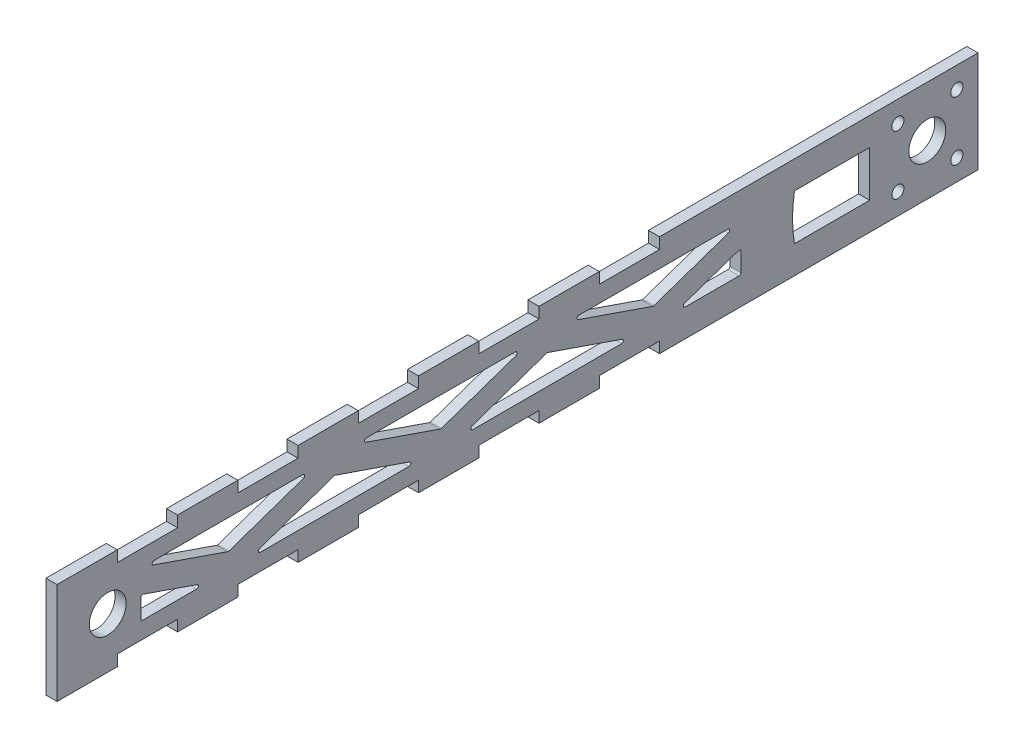
SolidWorks part; units mm, degrees
other "Markup1"
sketch "Sketch2" plane through (3, 13.75, 150) normal (0.7954, 0.3724, 0.4781) x (0.4726, 0.1125, -0.874)
ref_plane "Front Plane" through (0, 0, 0) normal (0, 0, 1) x (1, 0, 0)
ref_plane "Top Plane" through (0, 0, 0) normal (0, 1, 0) x (1, 0, 0)
ref_plane "Right Plane" through (0, 0, 0) normal (1, 0, 0) x (0, 0, -1)
sketch "Sketch1" plane through (0, 0, 0) normal (1, 0, 0) x (0, 0, -1)
  line L0 (71.25, -13.75) -> (71.25, 13.75) construction
  line L1 (-125, -13.75) -> (125, -13.75)
  line L2 (-125, -13.75) -> (-125, 13.75)
  line L3 (-125, 13.75) -> (125, 13.75)
  line L4 (125, -13.75) -> (125, 13.75)
  line L5 (-125, -13.75) -> (125, 13.75) construction
  line L6 (-125, 13.75) -> (125, -13.75) construction
  line L7 (103.25, -8) -> (119.25, -8) construction
  line L8 (103.25, -8) -> (103.25, 8) construction
  line L9 (103.25, 8) -> (119.25, 8) construction
  line L10 (119.25, -8) -> (119.25, 8) construction
  line L11 (103.25, -8) -> (119.25, 8) construction
  line L12 (103.25, 8) -> (119.25, -8) construction
  line L13 (-125, 10.75) -> (-108.6458, 10.75) construction
  line L14 (-108.6458, 10.75) -> (-92.2917, 10.75)
  line L15 (-108.6458, 10.75) -> (-108.6458, 13.75)
  line L16 (-108.6458, 13.75) -> (-92.2917, 13.75)
  line L17 (-92.2917, 10.75) -> (-92.2917, 13.75)
  line L18 (-108.6458, 10.75) -> (-92.2917, 13.75) construction
  line L19 (-108.6458, 13.75) -> (-92.2917, 10.75) construction
  line L20 (-75.9375, 10.75) -> (-59.5833, 10.75)
  line L21 (-75.9375, 10.75) -> (-75.9375, 13.75)
  line L22 (-75.9375, 13.75) -> (-59.5833, 13.75)
  line L23 (-59.5833, 10.75) -> (-59.5833, 13.75)
  line L24 (-75.9375, 10.75) -> (-59.5833, 13.75) construction
  line L25 (-75.9375, 13.75) -> (-59.5833, 10.75) construction
  line L26 (-43.2292, 10.75) -> (-26.875, 10.75)
  line L27 (-43.2292, 10.75) -> (-43.2292, 13.75)
  line L28 (-43.2292, 13.75) -> (-26.875, 13.75)
  line L29 (-26.875, 10.75) -> (-26.875, 13.75)
  line L30 (-43.2292, 10.75) -> (-26.875, 13.75) construction
  line L31 (-43.2292, 13.75) -> (-26.875, 10.75) construction
  line L32 (-10.5208, 10.75) -> (5.8333, 10.75)
  line L33 (-10.5208, 10.75) -> (-10.5208, 13.75)
  line L34 (-10.5208, 13.75) -> (5.8333, 13.75)
  line L35 (5.8333, 10.75) -> (5.8333, 13.75)
  line L36 (-10.5208, 10.75) -> (5.8333, 13.75) construction
  line L37 (-10.5208, 13.75) -> (5.8333, 10.75) construction
  line L38 (22.1875, 10.75) -> (38.5417, 10.75)
  line L39 (22.1875, 10.75) -> (22.1875, 13.75)
  line L40 (22.1875, 13.75) -> (38.5417, 13.75)
  line L41 (38.5417, 10.75) -> (38.5417, 13.75)
  line L42 (22.1875, 10.75) -> (38.5417, 13.75) construction
  line L43 (22.1875, 13.75) -> (38.5417, 10.75) construction
  line L44 (54.8958, 10.75) -> (71.25, 10.75)
  line L45 (54.8958, 10.75) -> (54.8958, 13.75)
  line L46 (54.8958, 13.75) -> (71.25, 13.75)
  line L47 (71.25, 10.75) -> (71.25, 13.75)
  line L48 (54.8958, 10.75) -> (71.25, 13.75) construction
  line L49 (54.8958, 13.75) -> (71.25, 10.75) construction
  line L50 (-92.2917, 10.75) -> (-75.9375, 10.75) construction
  line L51 (-59.5833, 10.75) -> (-43.2292, 10.75) construction
  line L52 (-26.875, 10.75) -> (-10.5208, 10.75) construction
  line L53 (5.8333, 10.75) -> (22.1875, 10.75) construction
  line L54 (38.5417, 10.75) -> (54.8958, 10.75) construction
  line L55 (75.1778, -6.2) -> (95.5778, -6.2)
  line L56 (-125, 0) -> (125, 0) construction
  line L57 (54.8958, -13.75) -> (71.25, -13.75)
  line L58 (71.25, -10.75) -> (71.25, -13.75)
  line L59 (54.8958, -10.75) -> (71.25, -10.75)
  line L60 (54.8958, -10.75) -> (54.8958, -13.75)
  line L61 (22.1875, -13.75) -> (38.5417, -13.75)
  line L62 (38.5417, -10.75) -> (38.5417, -13.75)
  line L63 (22.1875, -10.75) -> (38.5417, -10.75)
  line L64 (22.1875, -10.75) -> (22.1875, -13.75)
  line L65 (-10.5208, -13.75) -> (5.8333, -13.75)
  line L66 (5.8333, -10.75) -> (5.8333, -13.75)
  line L67 (-10.5208, -10.75) -> (5.8333, -10.75)
  line L68 (-10.5208, -10.75) -> (-10.5208, -13.75)
  line L69 (-43.2292, -13.75) -> (-26.875, -13.75)
  line L70 (-26.875, -10.75) -> (-26.875, -13.75)
  line L71 (-43.2292, -10.75) -> (-26.875, -10.75)
  line L72 (-43.2292, -10.75) -> (-43.2292, -13.75)
  line L73 (-75.9375, -13.75) -> (-59.5833, -13.75)
  line L74 (-59.5833, -10.75) -> (-59.5833, -13.75)
  line L75 (-75.9375, -10.75) -> (-59.5833, -10.75)
  line L76 (-75.9375, -10.75) -> (-75.9375, -13.75)
  line L77 (-108.6458, -13.75) -> (-92.2917, -13.75)
  line L78 (-92.2917, -10.75) -> (-92.2917, -13.75)
  line L79 (-108.6458, -10.75) -> (-92.2917, -10.75)
  line L80 (-108.6458, -10.75) -> (-108.6458, -13.75)
  line L81 (95.5778, -6.2) -> (95.5778, 6.2)
  line L82 (95.5778, 6.2) -> (75.1778, 6.2)
  circle A0 centre (103.25, 8) radius 1.65
  circle A1 centre (119.25, 8) radius 1.65
  circle A2 centre (119.25, -8) radius 1.65
  circle A3 centre (103.25, -8) radius 1.65
  circle A4 centre (111.25, 0) radius 5
  circle A5 centre (-111.25, 0) radius 5
  arc A6 (75.1778, -6.2) -> (75.1778, 6.2) centre (111.25, 0) cw
  point P0 (0, 0)
  point P6 (111.25, 0)
  point P19 (-100.4687, 12.25)
  point P26 (-67.7604, 12.25)
  point P31 (-35.0521, 12.25)
  point P36 (-2.3437, 12.25)
  point P41 (30.3646, 12.25)
  point P46 (63.0729, 12.25)
  point P83 (95.5778, 0)
  dimension "D2" = 3.3
  dimension "D3" = 10
  dimension "D7" = 10
  dimension "D1" = 16
  dimension "D4" = 13.75
  dimension "D5" = 27.5
  dimension "D6" = 250
  dimension "D8" = 13.75
  dimension "D9" = 40
  dimension "D10" = 3
  dimension "D11" = 15.6722
  dimension "D12" = 20.4
  dimension "D13" = 12.4
extrude "Boss-Extrude1" add sketch "Sketch1" along normal blind 3 contours L80 L79 L78 L1 L76 L75 L74 L72 L71 L70 L68 L67 L66 L64 L63 L62 L60 L59 L58 L4 L3 L47 L44 L45 L41 L38 L39 L35 L32 L33 L29 L26 L27 L23 L20 L21 L17 L14 L15 L2 | L44 L47 L3 L45 | L59 L60 L1 L58
sketch "Sketch3" plane through (3, 0, 0) normal (1, 0, 0) x (0, 0, -1)
  line L0 (-101.6617, 6.25) -> (-102.25, 6.25) construction
  line L1 (-102.25, -6.25) -> (60.6489, -6.25)
  line L2 (-102.25, -6.25) -> (-102.25, 6.25)
  line L3 (-102.25, 6.25) -> (60.6489, 6.25)
  line L4 (60.6489, -6.25) -> (60.6489, 6.25)
  line L5 (-102.25, -6.25) -> (60.6489, 6.25) construction
  line L6 (-102.25, 6.25) -> (60.6489, -6.25) construction
  line L7 (-102.25, 6.25) -> (-102.25, 10.75) construction
  line L8 (60.6489, 6.25) -> (60.0605, 6.25) construction
  line L9 (-102.25, -6.25) -> (-102.25, -10.75) construction
  line L10 (-102.25, 0) -> (-102.25, 6.25) construction
  line L11 (-102.25, 0) -> (-116.25, 0) construction
  line L12 (60.6489, 0) -> (74.6489, 0) construction
  line L13 (-108.6458, -10.75) -> (-92.2917, -10.75) construction
  line L14 (-102.25, 0) -> (-84.1399, -6.25)
  line L15 (-101.6617, 6.25) -> (-78.4807, -1.75)
  line L16 (-78.4807, -1.75) -> (-55.2998, 6.25)
  line L17 (-72.8216, -6.25) -> (-49.6407, 1.75)
  line L18 (-49.6407, 1.75) -> (-26.4597, -6.25)
  line L19 (-15.1414, -6.25) -> (8.0395, 1.75)
  line L20 (8.0395, 1.75) -> (31.2204, -6.25)
  line L21 (42.5388, -6.25) -> (60.6489, 0)
  line L22 (-84.1399, -6.25) -> (-72.8216, -6.25) construction
  line L23 (-55.2998, 6.25) -> (-43.9815, 6.25) construction
  line L24 (-43.9815, 6.25) -> (-20.8006, -1.75)
  line L25 (-20.8006, -1.75) -> (2.3803, 6.25)
  line L26 (13.6987, 6.25) -> (36.8796, -1.75)
  line L27 (36.8796, -1.75) -> (60.0605, 6.25)
  line L28 (-26.4597, -6.25) -> (-15.1414, -6.25) construction
  line L29 (2.3803, 6.25) -> (13.6987, 6.25) construction
  line L30 (31.2204, -6.25) -> (42.5388, -6.25) construction
  line L31 (60.6489, 0) -> (60.6489, 6.25) construction
  circle A0 centre (-111.25, 0) radius 5 construction
  arc A1 (75.1778, 6.2) -> (75.1778, -6.2) centre (111.25, 0) ccw construction
  point P0 (-20.8006, 0)
  dimension "D1" = 4.5
  dimension "D2" = 14
  dimension "D3" = 6.1
  dimension "D4" = 8
extrude "Cut-Extrude1" cut sketch "Sketch3" against normal blind 3 contours L14 L2 L1 | L15 L16 L3 | L18 L17 L1 | L24 L25 L3 | L20 L19 L1 | L26 L27 L3 | L21 L1 L4
fillet "Fillet1" radius 0.5 21 edges at (1.5, -6.25, -42.5388) (1.5, 0, -60.6489) (1.5, -6.25, -60.6489) (1.5, -6.25, 26.4597) (1.5, -6.25, 72.8216) (1.5, -6.25, -31.2204) (1.5, -6.25, 15.1414) (1.5, 1.75, -8.0395) (1.5, 6.25, 43.9815) (1.5, 6.25, -13.6987) (1.5, -1.75, -36.8796) (1.5, -1.75, 20.8006) (1.5, 6.25, -60.0605) (1.5, 6.25, -2.3803) (1.5, 1.75, 49.6407) (1.5, 6.25, 55.2998) (1.5, -1.75, 78.4807) (1.5, 6.25, 101.6617) (1.5, 0, 102.25) (1.5, -6.25, 84.1399) (1.5, -6.25, 102.25)
